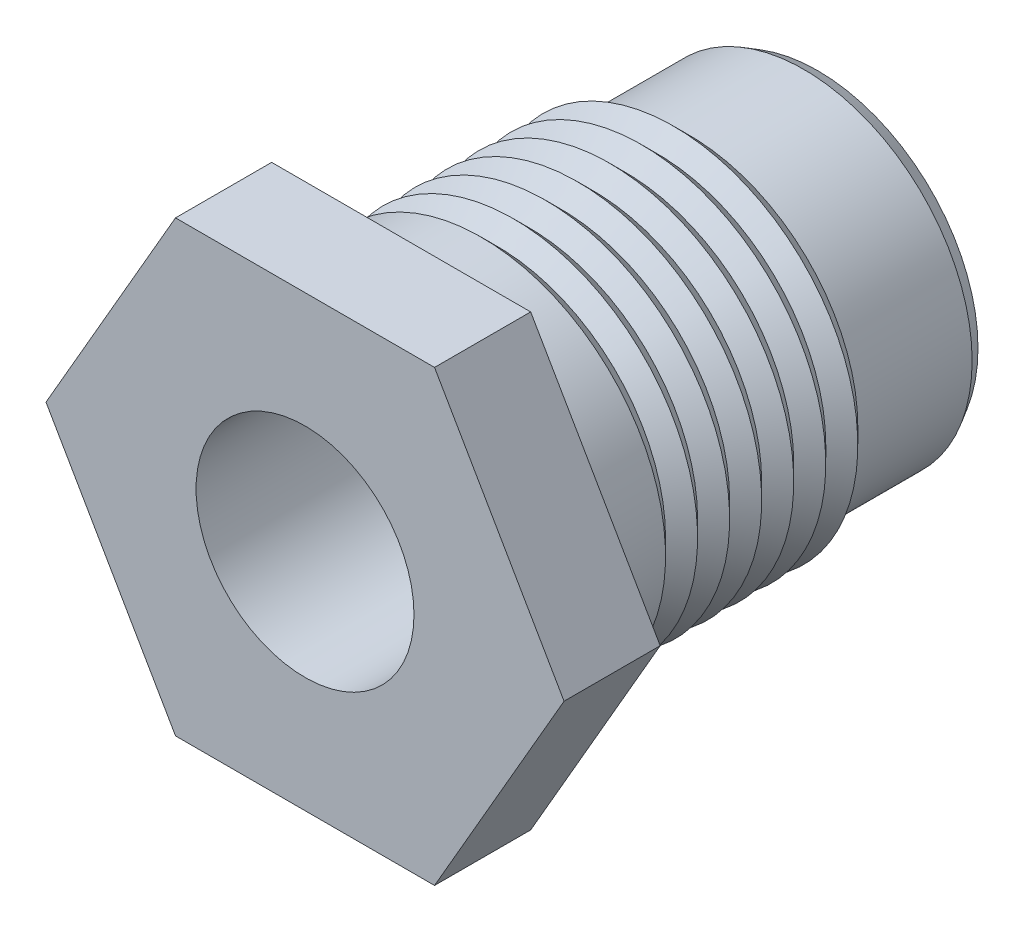
SolidWorks part; units mm, degrees
ref_plane "Plane1" through (0, 0, 0) normal (0, 0, 1) x (1, 0, 0)
ref_plane "Plane2" through (0, 0, 0) normal (0, 1, 0) x (1, 0, 0)
ref_plane "Plane3" through (0, 0, 0) normal (1, 0, 0) x (0, 0, -1)
sketch "Sketch1" plane through (0, 0, 0) normal (0, 0, 1) x (1, 0, 0)
  line L1 (8.0829, 0) -> (4.0415, 7)
  line L2 (4.0415, 7) -> (-4.0415, 7)
  line L3 (-4.0415, 7) -> (-8.0829, 0)
  line L4 (-8.0829, 0) -> (-4.0415, -7)
  line L5 (-4.0415, -7) -> (4.0415, -7)
  line L6 (4.0415, -7) -> (8.0829, 0)
  circle A0 centre (0, 0) radius 7 construction
  circle A1 centre (0, 0) radius 3.4
  dimension "D2" = 6.8
  dimension "D1" = 14
extrude "Extrude1" add sketch "Sketch1" along normal blind 16
cosmetic thread "Cosmetic Thread1" parameters "D2"=8
sketch "Sketch2" plane through (0, 0, 0) normal (0, 1, 0) x (1, 0, 0)
  line L0 (5.75, -4.5) -> (5.75, -12.6)
  line L1 (4.0415, 0) -> (-4.0415, 0) construction
  line L2 (5.75, -4.5) -> (5.25, -4)
  line L3 (5.25, -4) -> (5.25, -0.433)
  line L4 (6.15, -13) -> (8.0829, -13)
  line L5 (8.0829, -16) -> (8.0829, 0) construction
  line L6 (8.0829, -16) -> (4.0415, -16) construction
  line L7 (0, 0) -> (0, -16) construction
  line L8 (4.0415, -16) -> (-4.0415, -16) construction
  line L9 (5, 0) -> (8.0829, 0)
  line L10 (8.0829, 0) -> (4.0415, 0) construction
  line L11 (8.0829, 0) -> (8.0829, -13)
  line L12 (5, 0) -> (5.25, -0.433)
  arc A0 (5.75, -12.6) -> (6.15, -13) centre (6.15, -12.6) ccw
  dimension "D3" = 0.4
  dimension "D1" = 3
  dimension "D2" = 11.5
  dimension "D4" = 10.5
  dimension "D5" = 4
  dimension "D6" = 45
  dimension "D7" = 30
  dimension "D8" = 10
revolve "Cut-Revolve1" cut sketch "Sketch2" angle 360 about L7
sketch "Sketch4" plane through (0, 0, 0) normal (0, 1, 0) x (1, 0, 0)
  line L0 (0, 0) -> (0, -16) construction
  line L1 (4.0415, -16) -> (-4.0415, -16) construction
  line L2 (5.75, -4.5) -> (5.75, -5.5)
  line L3 (5.75, -12.6) -> (5.75, -4.5) construction
  line L4 (5.75, -4.5) -> (5.25, -5)
  line L5 (5.25, -5) -> (5.75, -5.5)
  line L6 (5.75, -5) -> (5.25, -5) construction
  line L7 (-5.75, -4.5) -> (5.75, -4.5) construction
  dimension "D1" = 0.5
  dimension "D2" = 0.5
  dimension "D3" = 90
revolve "Cut-Revolve2" cut sketch "Sketch4" angle 360 about L0
pattern_linear "LPattern2" count 6 spacing 1 along (0, 0, 1) of "Cut-Revolve2"
